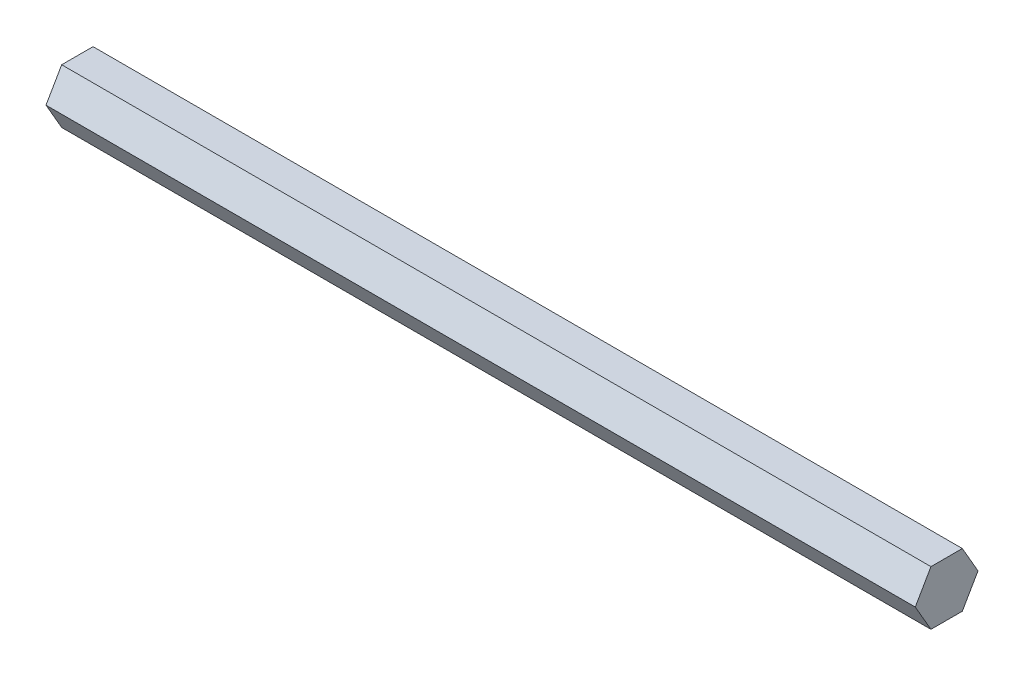
SolidWorks part; units mm, degrees
ref_plane "Front Plane" through (0, 0, 0) normal (0, 0, 1) x (1, 0, 0)
ref_plane "Top Plane" through (0, 0, 0) normal (0, 1, 0) x (1, 0, 0)
ref_plane "Right Plane" through (0, 0, 0) normal (1, 0, 0) x (0, 0, -1)
sketch "Sketch1" plane through (0, 0, 0) normal (1, 0, 0) x (0, 0, -1)
  line L1 (7.3323, 0) -> (3.6662, 6.35)
  line L2 (3.6662, 6.35) -> (-3.6662, 6.35)
  line L3 (-3.6662, 6.35) -> (-7.3323, 0)
  line L4 (-7.3323, 0) -> (-3.6662, -6.35)
  line L5 (-3.6662, -6.35) -> (3.6662, -6.35)
  line L6 (3.6662, -6.35) -> (7.3323, 0)
  circle A0 centre (0, 0) radius 6.35 construction
extrude "Boss-Extrude1" add sketch "Sketch1" along normal blind 203.2
